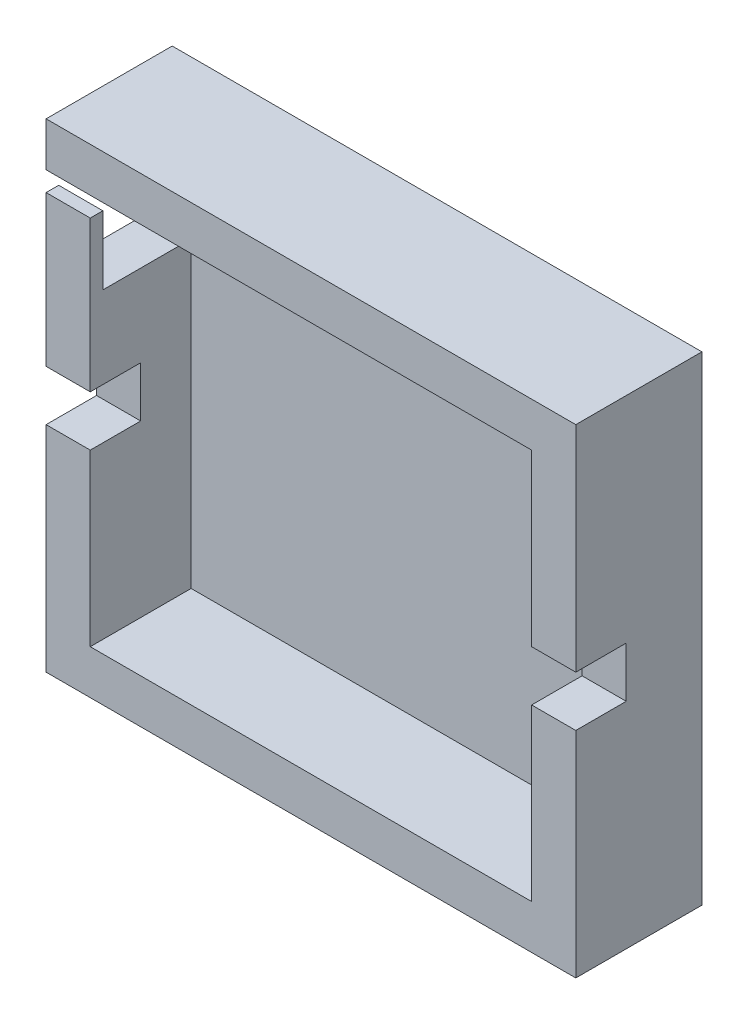
SolidWorks part; units mm, degrees
ref_plane "前视基准面" through (0, 0, 0) normal (0, 0, 1) x (1, 0, 0)
ref_plane "上视基准面" through (0, 0, 0) normal (0, 1, 0) x (1, 0, 0)
ref_plane "右视基准面" through (0, 0, 0) normal (1, 0, 0) x (0, 0, -1)
sketch "草图1" plane through (0, 0, 0) normal (0, 0, 1) x (1, 0, 0)
  line L1 (0, 0) -> (35, 0) construction
  line L2 (0, 0) -> (0, 31) construction
  line L3 (0, 31) -> (35, 31) construction
  line L4 (35, 0) -> (35, 31) construction
  line L5 (0, 0) -> (-3.5, 0) construction
  line L6 (0, 0) -> (0, -3.5) construction
  line L7 (0, -3.5) -> (-3.5, -3.5) construction
  line L8 (-3.5, 0) -> (-3.5, -3.5) construction
  line L9 (-3.5, -3.5) -> (38.5, -3.5)
  line L10 (-3.5, -3.5) -> (-3.5, 34.5)
  line L11 (-3.5, 34.5) -> (38.5, 34.5)
  line L12 (38.5, -3.5) -> (38.5, 34.5)
  dimension "D1" = 35
  dimension "D2" = 31
  dimension "D3" = 3.5
  dimension "D4" = 3.5
  dimension "D5" = 38
  dimension "D6" = 42
extrude "凸台-拉伸1" add sketch "草图1" along normal blind 2
sketch "草图2" plane through (0, 0, 2) normal (0, 0, 1) x (1, 0, 0)
  line L1 (0, 0) -> (35, 0)
  line L2 (0, 0) -> (0, 31)
  line L3 (0, 31) -> (35, 31)
  line L4 (35, 0) -> (35, 31)
  line L5 (-3.5, -3.5) -> (38.5, -3.5)
  line L6 (-3.5, -3.5) -> (-3.5, 34.5)
  line L7 (-3.5, 34.5) -> (38.5, 34.5)
  line L8 (38.5, -3.5) -> (38.5, 34.5)
  dimension "D1" = 31
  dimension "D2" = 35
  dimension "D3" = 42
  dimension "D4" = 38
extrude "凸台-拉伸2" add sketch "草图2" along normal blind 8
sketch "草图3" plane through (-3.5, 0, 0) normal (-1, 0, 0) x (0, 0, 1)
  line L0 (10, 34.5) -> (10, -3.5) construction
  line L1 (0, 34.5) -> (2, 34.5)
  line L2 (0, 34.5) -> (0, 31)
  line L3 (0, 31) -> (2, 31)
  line L4 (2, 34.5) -> (2, 31)
  line L5 (2, 31) -> (9, 31)
  line L6 (2, 31) -> (2, 24)
  line L7 (2, 24) -> (9, 24)
  line L8 (9, 31) -> (9, 24)
  line L9 (9, 31) -> (10, 31)
  line L10 (9, 31) -> (9, 29.4354)
  line L11 (9, 29.4354) -> (10, 29.4354)
  line L12 (10, 31) -> (10, 29.4354)
  line M6 (10, -3.5) -> (10, 34.5)
  dimension "D1" = 2
  dimension "D2" = 3.5
  dimension "D3" = 7
extrude "切除-拉伸1" cut sketch "草图3" against normal blind 6.5 contours L6 L7 L5 M6 | L10 L9 L12 L11
sketch "草图6" plane through (0, 0, 10) normal (0, 0, 1) x (1, 0, 0)
  line L0 (-3.5, 34.5) -> (-3.5, -3.5) construction
  line L1 (35, 15.5) -> (35, 17.5)
  line L2 (0, 31) -> (0, 0) construction
  line L3 (0, 15.5) -> (0, 17.5)
  line L4 (0, 17.5) -> (-3.5, 17.5)
  line L5 (0, 17.5) -> (0, 13.5)
  line L6 (0, 13.5) -> (-3.5, 13.5)
  line L7 (-3.5, 17.5) -> (-3.5, 13.5)
  line L8 (35, 0) -> (35, 31) construction
  line L9 (38.5, -3.5) -> (38.5, 34.5) construction
  line L10 (35, 17.5) -> (38.5, 17.5)
  line L11 (35, 17.5) -> (35, 13.5)
  line L12 (35, 13.5) -> (38.5, 13.5)
  line L13 (38.5, 17.5) -> (38.5, 13.5)
  line M9 (35, 31) -> (35, 0)
  line M11 (0, 0) -> (0, 31)
  line M15 (-3.5, 34.5) -> (-3.5, -3.5)
  line M17 (38.5, -3.5) -> (38.5, 34.5)
  dimension "D1" = 4
  dimension "D2" = 2
extrude "切除-拉伸3" cut sketch "草图6" against normal blind 4 contours L6 L4 M11 M15 | L12 L10 M9 M17
sketch "草图7" plane through (0, 0, 0) normal (0, 0, -1) x (-1, 0, 0)
  line L0 (-5, 34.5) -> (-5, 23.9)
  line L1 (-38.5, 34.5) -> (3.5, 34.5) construction
  line L2 (-28, 34.5) -> (-28, 28.1)
  line L3 (-28, 28.1) -> (-38.5, 28.1)
  line L4 (-38.5, -3.5) -> (-38.5, 34.5) construction
  line L5 (-5, 23.9) -> (3.5, 23.9)
  line L6 (3.5, 34.5) -> (3.5, -3.5) construction
  line L8 (-28, 28.1) -> (-5, 28.1)
  line L9 (-28, 28.1) -> (-28, 23.9)
  line L10 (-28, 23.9) -> (-5, 23.9)
  line L11 (-5, 28.1) -> (-5, 23.9)
  dimension "D1" = 10.6
  dimension "D2" = 6.4
  dimension "D3" = 10.5
  dimension "D4" = 8.5
extrude "切除-拉伸4" cut sketch "草图7" against normal blind 10 contours L9 L10 L0 L8
